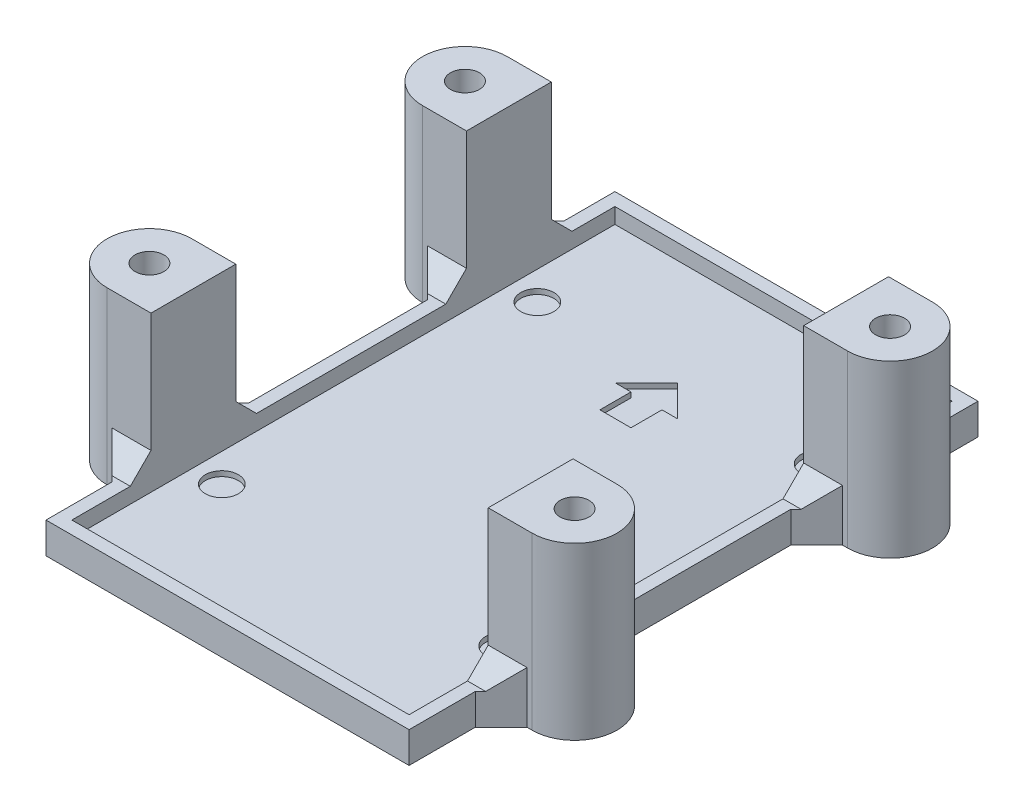
SolidWorks part; units mm, degrees
ref_plane "Front Plane" through (0, 0, 0) normal (0, 0, 1) x (1, 0, 0)
ref_plane "Top Plane" through (0, 0, 0) normal (0, 1, 0) x (1, 0, 0)
ref_plane "Right Plane" through (0, 0, 0) normal (1, 0, 0) x (0, 0, -1)
sketch "Template" plane through (0, 0, 0) normal (0, 1, 0) x (1, 0, 0)
  line L0 (2.5, 52) -> (2.5, 0) construction
  line L1 (0, 0) -> (32.1, 0) construction
  line L2 (0, 0) -> (0, 52) construction
  line L3 (0, 52) -> (32.1, 52) construction
  line L4 (32.1, 0) -> (32.1, 52) construction
  line L5 (29.6, 52) -> (29.6, 0) construction
  line L6 (0, 11.5) -> (32.1, 11.5) construction
  line L7 (0, 42) -> (32.1, 42) construction
  line L8 (-20.7027, 16.9977) -> (-20.7027, 39.1419)
  line L9 (-20.7027, 39.1419) -> (-24.8089, 35.0356)
  line L10 (-20.7027, 39.1419) -> (-16.5965, 35.0356)
  dimension "D1" = 32.1
  dimension "D2" = 52
  dimension "D3" = 30.5
  dimension "D4" = 10
  dimension "D5" = 2.5
  dimension "D6" = 2.5
sketch "Sketch2" plane through (0, 0, 0) normal (0, 1, 0) x (1, 0, 0)
  line L0 (-1.5, -1.5) -> (-1.5, 4.9)
  line L1 (-1.5, 53.5) -> (33.6, 53.5)
  line L3 (-1.5, -1.5) -> (33.6, -1.5)
  line L5 (-4, 7.4) -> (-4.5, 7.4)
  line L6 (-4.5, 7.4) -> (-4.5, 15.6) construction
  line L7 (-4.5, 15.6) -> (-4, 15.6)
  line L8 (-1.5, 18.1) -> (-1.5, 35.4)
  line L9 (-4, 37.9) -> (-4.5, 37.9)
  line L10 (-4.5, 37.9) -> (-4.5, 46.1) construction
  line L11 (-4.5, 46.1) -> (-4, 46.1)
  line L12 (-1.5, 48.6) -> (-1.5, 53.5)
  line L13 (33.6, 53.5) -> (33.6, 48.6)
  line L14 (36.1, 46.1) -> (36.6, 46.1)
  line L15 (36.6, 46.1) -> (36.6, 37.9) construction
  line L16 (36.6, 37.9) -> (36.1, 37.9)
  line L17 (33.6, 35.4) -> (33.6, 18.1)
  line L18 (36.1, 15.6) -> (36.6, 15.6)
  line L19 (36.6, 15.6) -> (36.6, 7.4) construction
  line L20 (36.6, 7.4) -> (36.1, 7.4)
  line L21 (33.6, 4.9) -> (33.6, -1.5)
  line L22 (-4.5, 42) -> (0, 42) construction
  line L27 (32.1, 42) -> (36.6, 42) construction
  line L28 (32.1, 11.5) -> (36.6, 11.5) construction
  line L29 (0, 11.5) -> (-4.5, 11.5) construction
  line L33 (32.1, 0) -> (32.1, 52) construction
  line L34 (-4, 46.1) -> (-1.5, 48.6)
  line L35 (-4, 15.6) -> (-1.5, 18.1)
  line L36 (33.6, 18.1) -> (36.1, 15.6)
  line L37 (36.1, 37.9) -> (33.6, 35.4)
  line L38 (33.6, 48.6) -> (36.1, 46.1)
  line L39 (-1.5, 35.4) -> (-4, 37.9)
  line L40 (36.1, 7.4) -> (33.6, 4.9)
  line L41 (-1.5, 4.9) -> (-4, 7.4)
  line L42 (0, 0) -> (32.1, 0) construction
  line L43 (0, 52) -> (32.1, 52) construction
  line L44 (0, 0) -> (0, 52) construction
  arc A0 (-4.5, 46.1) -> (-4.5, 37.9) centre (-4.5, 42) ccw
  arc A1 (-4.5, 15.6) -> (-4.5, 7.4) centre (-4.5, 11.5) ccw
  arc A2 (36.6, 46.1) -> (36.6, 37.9) centre (36.6, 42) cw
  arc A3 (36.6, 15.6) -> (36.6, 7.4) centre (36.6, 11.5) cw
  circle A4 centre (-4.5, 42) radius 1.4
  circle A5 centre (-4.5, 11.5) radius 1.4
  circle A6 centre (36.6, 11.5) radius 1.4
  circle A7 centre (36.6, 42) radius 1.4
  point P17 (33.6, 15.6)
  point P20 (33.1, 7.4)
  dimension "D1" = 2.8
  dimension "D2" = 2.7
  dimension "D3" = 1.5
  dimension "D4" = 1.5
  dimension "D5" = 1.5
  dimension "D6" = 1.5
  dimension "D7" = 4.5
  dimension "D8" = 2.5
  dimension "D9" = 2.5
extrude "Boss-Extrude1" add sketch "Sketch2" against normal blind 1.5
sketch "Sketch5" plane through (0, 0, 0) normal (0, 1, 0) x (1, 0, 0)
  line L0 (2.5, 52) -> (2.5, 0) construction
  line L1 (29.6, 52) -> (29.6, 0) construction
  line L2 (0, 11.5) -> (32.1, 11.5) construction
  line L3 (0, 42) -> (32.1, 42) construction
  line L4 (14.55, 36) -> (17.55, 36)
  line L5 (17.55, 36) -> (17.55, 39)
  line L6 (17.55, 39) -> (19.05, 39)
  line L7 (19.05, 39) -> (16.05, 42)
  line L8 (16.05, 42) -> (13.05, 39)
  line L9 (13.05, 39) -> (14.55, 39)
  line L10 (14.55, 39) -> (14.55, 36)
  circle A0 centre (2.5, 42) radius 1.6
  circle A1 centre (29.6, 42) radius 1.6
  circle A2 centre (29.6, 11.5) radius 1.6
  circle A3 centre (2.5, 11.5) radius 1.6
  point P24 (16.05, 42)
  dimension "D1" = 3.2
  dimension "D2" = 3
  dimension "D3" = 3
  dimension "D4" = 3
extrude "Cut-Extrude1" cut sketch "Sketch5" against normal blind 0.5
sketch "Sketch3" plane through (0, 0, 0) normal (0, 1, 0) x (1, 0, 0)
  line L0 (-1.5, 53.5) -> (33.6, 53.5)
  line L2 (36.1, 46.1) -> (36.6, 46.1)
  line L3 (36.6, 46.1) -> (36.6, 37.9) construction
  line L4 (36.6, 37.9) -> (36.1, 37.9)
  line L6 (36.1, 15.6) -> (36.6, 15.6)
  line L7 (36.6, 15.6) -> (36.6, 7.4) construction
  line L8 (36.6, 7.4) -> (36.1, 7.4)
  line L10 (33.6, -1.5) -> (-1.5, -1.5)
  line L12 (-4, 7.4) -> (-4.5, 7.4)
  line L13 (-4.5, 7.4) -> (-4.5, 15.6) construction
  line L14 (-4.5, 15.6) -> (-4, 15.6)
  line L16 (-4, 37.9) -> (-4.5, 37.9)
  line L17 (-4.5, 37.9) -> (-4.5, 46.1) construction
  line L18 (-4.5, 46.1) -> (-4, 46.1)
  line L20 (0, 52) -> (32.1, 52) construction
  line L25 (-0.25, 52.25) -> (32.35, 52.25)
  line L26 (-0.25, 52.25) -> (-0.25, -0.25)
  line L27 (-0.25, -0.25) -> (32.35, -0.25)
  line L28 (32.35, 52.25) -> (32.35, -0.25)
  line L29 (0, 0) -> (0, 52) construction
  line L30 (32.1, 0) -> (32.1, 52) construction
  line L31 (0, 0) -> (32.1, 0) construction
  line L32 (-1.5, 18.1) -> (-4, 15.6) construction
  line L33 (-4, 7.4) -> (-1.5, 4.9) construction
  line L34 (36.1, 46.1) -> (33.6, 48.6) construction
  line L35 (-4, 46.1) -> (-1.5, 48.6)
  line L36 (-1.5, 48.6) -> (-1.5, 53.5)
  line L37 (33.6, 53.5) -> (33.6, 48.6)
  line L38 (33.6, 48.6) -> (36.1, 46.1)
  line L39 (36.1, 37.9) -> (33.6, 35.4)
  line L40 (33.6, 35.4) -> (33.6, 18.1)
  line L41 (33.6, 18.1) -> (36.1, 15.6)
  line L42 (33.6, -1.5) -> (33.6, 4.9)
  line L43 (33.6, 4.9) -> (36.1, 7.4)
  line L44 (-4, 7.4) -> (-1.5, 4.9)
  line L45 (-1.5, 4.9) -> (-1.5, -1.5)
  line L46 (-4, 15.6) -> (-1.5, 18.1)
  line L47 (-1.5, 18.1) -> (-1.5, 35.4)
  line L48 (-1.5, 35.4) -> (-4, 37.9)
  arc A0 (-4.5, 46.1) -> (-4.5, 37.9) centre (-4.5, 42) ccw
  arc A1 (-4.5, 15.6) -> (-4.5, 7.4) centre (-4.5, 11.5) ccw
  arc A2 (36.6, 7.4) -> (36.6, 15.6) centre (36.6, 11.5) ccw
  arc A3 (36.6, 37.9) -> (36.6, 46.1) centre (36.6, 42) ccw
  circle A4 centre (-4.5, 42) radius 1.4
  circle A5 centre (36.6, 42) radius 1.4
  circle A6 centre (36.6, 11.5) radius 1.4
  circle A7 centre (-4.5, 11.5) radius 1.4
  circle A8 centre (-4.5, 11.5) radius 1.4 construction
  circle A9 centre (-4.5, 42) radius 1.4 construction
  circle A10 centre (36.6, 42) radius 1.4 construction
  circle A11 centre (36.6, 11.5) radius 1.4 construction
  dimension "D1" = 0.25
  dimension "D2" = 0.25
  dimension "D3" = 0.25
  dimension "D4" = 0.25
extrude "Boss-Extrude2" add sketch "Sketch3" along normal blind 1.5
sketch "Sketch4" plane through (0, 1.5, 0) normal (0, 1, 0) x (1, 0, 0)
  line L0 (-0.25, 52.25) -> (-0.25, -0.25) construction
  line L1 (-4.5, 46.1) -> (-0.25, 46.1)
  line L2 (-4.5, 46.1) -> (-4.5, 37.9) construction
  line L4 (-0.25, 46.1) -> (-0.25, 37.9)
  line L7 (-4.5, 15.6) -> (-4.5, 7.4) construction
  line L8 (-4.5, 7.4) -> (-0.25, 7.4)
  line L9 (-0.25, 15.6) -> (-0.25, 7.4)
  line L11 (32.35, 15.6) -> (32.35, 7.4)
  line L12 (32.35, 7.4) -> (36.6, 7.4)
  line L13 (36.6, 15.6) -> (36.6, 7.4) construction
  line L14 (32.35, 46.1) -> (36.6, 46.1)
  line L15 (32.35, 46.1) -> (32.35, 37.9)
  line L17 (36.6, 46.1) -> (36.6, 37.9) construction
  line L18 (32.35, -0.25) -> (32.35, 52.25) construction
  line L21 (36.6, 37.9) -> (32.35, 37.9)
  line L23 (32.35, 15.6) -> (36.6, 15.6)
  line L24 (-4.5, 37.9) -> (-0.25, 37.9)
  line L26 (-0.25, 15.6) -> (-4.5, 15.6)
  arc A0 (-4.5, 46.1) -> (-4.5, 37.9) centre (-4.5, 42) ccw
  arc A1 (-4.5, 15.6) -> (-4.5, 7.4) centre (-4.5, 11.5) ccw
  arc A2 (36.6, 7.4) -> (36.6, 15.6) centre (36.6, 11.5) ccw
  arc A3 (36.6, 46.1) -> (36.6, 37.9) centre (36.6, 42) cw
  circle A4 centre (-4.5, 42) radius 1.4
  circle A5 centre (-4.5, 11.5) radius 1.4
  circle A6 centre (36.6, 42) radius 1.4
  circle A7 centre (36.6, 11.5) radius 1.4
  circle A8 centre (-4.5, 42) radius 1.4 construction
  circle A9 centre (-4.5, 11.5) radius 1.4 construction
  circle A10 centre (36.6, 11.5) radius 1.4 construction
  circle A11 centre (36.6, 42) radius 1.4 construction
  arc A12 (-4.5, 15.6) -> (-4.5, 7.4) centre (-4.5, 11.5) ccw construction
extrude "Boss-Extrude3" add sketch "Sketch4" along normal blind 13.5
chamfer "Chamfer1" distance 2 angle 45 8 edges at (-2.125, 1.5, -46.1) (34.225, 1.5, -37.9) (34.225, 1.5, -46.1) (34.225, 1.5, -15.6) (34.225, 1.5, -7.4) (-2.125, 1.5, -7.4) (-2.125, 1.5, -15.6) (-2.125, 1.5, -37.9)
sketch "Sketch6" plane through (0, -1.5, 0) normal (0, -1, 0) x (1, 0, 0)
  line L0 (-4.5, -42) -> (0, -42) construction
  line L1 (-1.2668, -42) -> (-2.8834, -39.2)
  line L2 (-2.8834, -39.2) -> (-6.1166, -39.2)
  line L3 (-6.1166, -39.2) -> (-7.7332, -42)
  line L4 (-7.7332, -42) -> (-6.1166, -44.8)
  line L5 (-6.1166, -44.8) -> (-2.8834, -44.8)
  line L6 (-2.8834, -44.8) -> (-1.2668, -42)
  line L7 (33.3668, -42) -> (34.9834, -44.8)
  line L8 (34.9834, -44.8) -> (38.2166, -44.8)
  line L9 (38.2166, -44.8) -> (39.8332, -42)
  line L10 (39.8332, -42) -> (38.2166, -39.2)
  line L11 (38.2166, -39.2) -> (34.9834, -39.2)
  line L12 (34.9834, -39.2) -> (33.3668, -42)
  line L13 (-1.2668, -11.5) -> (-2.8834, -8.7)
  line L14 (-2.8834, -8.7) -> (-6.1166, -8.7)
  line L15 (-6.1166, -8.7) -> (-7.7332, -11.5)
  line L16 (-7.7332, -11.5) -> (-6.1166, -14.3)
  line L17 (-6.1166, -14.3) -> (-2.8834, -14.3)
  line L18 (-2.8834, -14.3) -> (-1.2668, -11.5)
  line L19 (33.3668, -11.5) -> (34.9834, -14.3)
  line L20 (34.9834, -14.3) -> (38.2166, -14.3)
  line L21 (38.2166, -14.3) -> (39.8332, -11.5)
  line L22 (39.8332, -11.5) -> (38.2166, -8.7)
  line L23 (38.2166, -8.7) -> (34.9834, -8.7)
  line L24 (34.9834, -8.7) -> (33.3668, -11.5)
  line L25 (32.1, -42) -> (36.6, -42) construction
  line L26 (32.1, -11.5) -> (36.6, -11.5) construction
  line L27 (0, -11.5) -> (-4.5, -11.5) construction
  circle A0 centre (-4.5, -42) radius 2.8 construction
  circle A1 centre (36.6, -42) radius 2.8 construction
  circle A2 centre (-4.5, -11.5) radius 2.8 construction
  circle A3 centre (36.6, -11.5) radius 2.8 construction
  dimension "D1" = 5.6
extrude "Cut-Extrude2" cut sketch "Sketch6" against normal blind 2.5 and the other way through all
